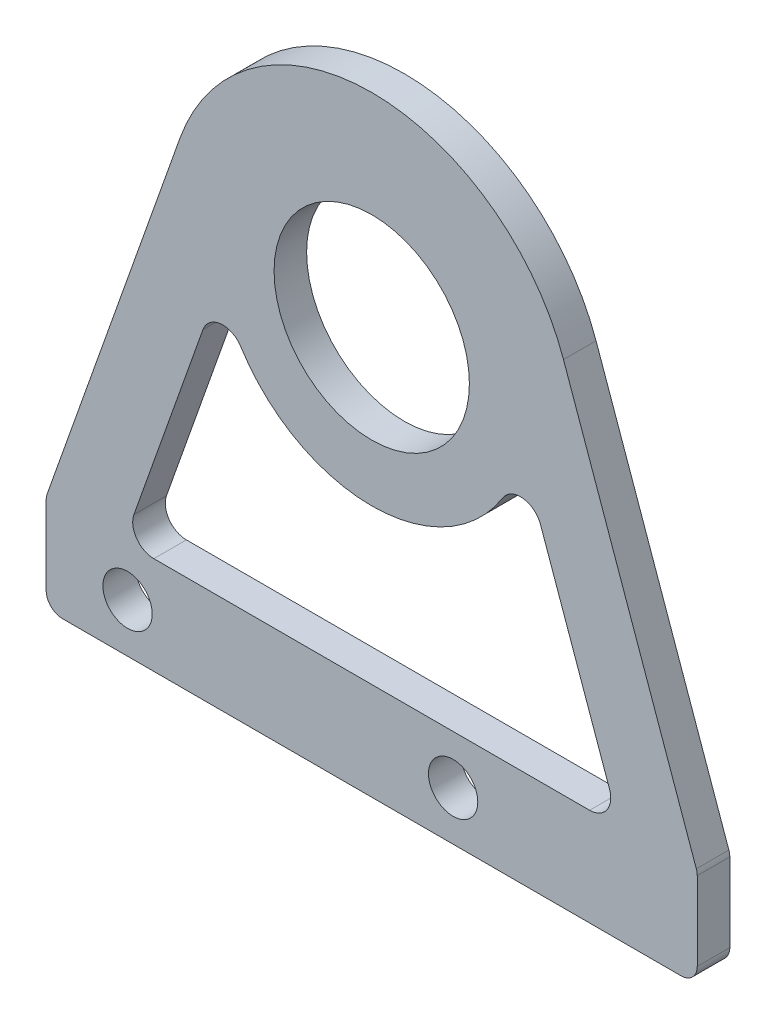
SolidWorks part; units mm, degrees
material "Thornel Mat VMA"
ref_plane "前视基准面" through (0, 0, 0) normal (0, 0, 1) x (1, 0, 0)
ref_plane "上视基准面" through (0, 0, 0) normal (0, 1, 0) x (1, 0, 0)
ref_plane "右视基准面" through (0, 0, 0) normal (1, 0, 0) x (0, 0, -1)
sketch "草图1" plane through (0, 0, 0) normal (0, 0, 1) x (1, 0, 0)
  line L0 (0, 0) -> (0, -25) construction
  line L1 (-20, -25) -> (20, -25)
  line L2 (20, -25) -> (20, -19)
  line L3 (20, -19) -> (11.7812, 4.1776)
  line L4 (-20, -19) -> (-11.7812, 4.1776)
  line L5 (-20, -25) -> (-20, -19)
  arc A0 (11.7812, 4.1776) -> (-11.7812, 4.1776) centre (0, 0) ccw
  circle A1 centre (0, 0) radius 6
  point P9 (0, -25)
  dimension "D1" = 12
  dimension "D2" = 25
  dimension "D3" = 40
  dimension "D4" = 6
  dimension "D5" = 25
extrude "凸台-拉伸1" add sketch "草图1" along normal blind 2
fillet "圆角1" radius 1 4 edges at (-20, -25, 1) (-20, -19, 1) (20, -19, 1) (20, -25, 1)
sketch "草图2" plane through (0, 0, 0) normal (0, 0, -1) x (-1, 0, 0)
  circle A0 centre (15, -22) radius 1.25 construction
  circle A1 centre (-5, -22) radius 1.25 construction
  circle A2 centre (15, -22) radius 1.25 construction
  circle A3 centre (-5, -22) radius 1.25 construction
  circle A4 centre (15, -22) radius 1.515
  circle A5 centre (-5, -22) radius 1.515
  dimension "D1" = 3.03
extrude "切除-拉伸1" cut sketch "草图2" against normal blind 10
sketch "草图3" plane through (0, 0, 0) normal (0, 0, -1) x (-1, 0, 0)
  line L0 (-9.2523, -2.1552) -> (-15.2255, -19)
  line L1 (-15.2255, -19) -> (15.2255, -19)
  line L2 (15.2255, -19) -> (9.2523, -2.1552)
  line L3 (11.7812, 4.1776) -> (19.9425, -18.8378) construction
  line L4 (-19.9425, -18.8378) -> (-11.7812, 4.1776) construction
  arc A0 (-9.2523, -2.1552) -> (9.2523, -2.1552) centre (0, 0) ccw
  circle A1 centre (0, 0) radius 6 construction
  circle A2 centre (-5, -22) radius 1.515 construction
  dimension "D1" = 3.5
  dimension "D2" = 4.5
  dimension "D3" = 4.5
  dimension "D4" = 3
extrude "切除-拉伸2" cut sketch "草图3" against normal blind 10
fillet "圆角2" radius 1.3 4 edges at (-9.2523, -2.1552, 1) (-15.2255, -19, 1) (15.2255, -19, 1) (9.2523, -2.1552, 1)
equation "\"D3@草图3\"=\"D2@草图3\""
